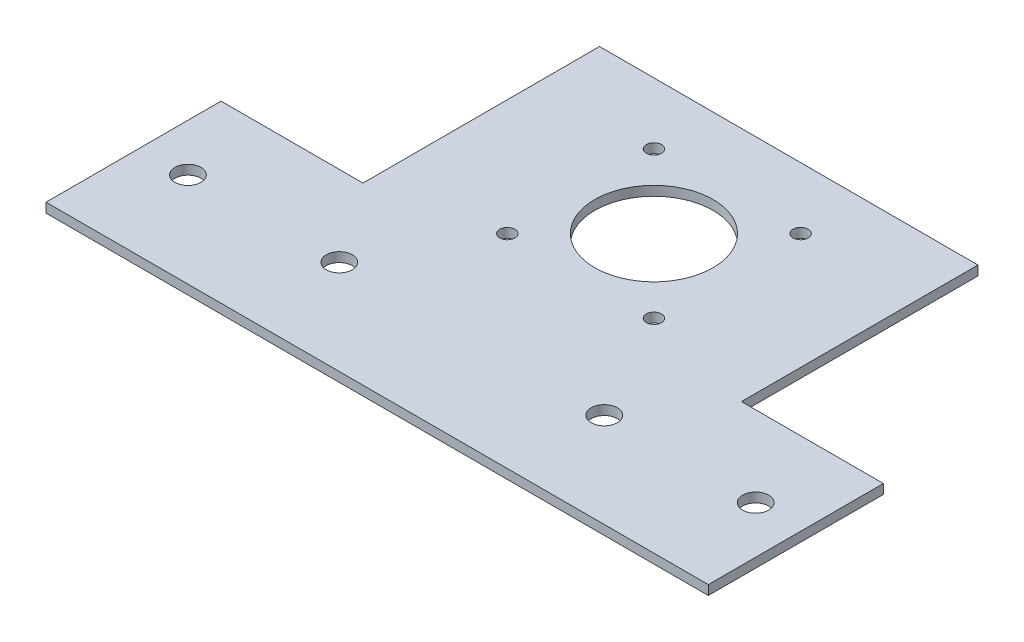
SolidWorks part; units mm, degrees
ref_plane "Plan de face" through (0, 0, 0) normal (0, 0, 1) x (1, 0, 0)
ref_plane "Plan de dessus" through (0, 0, 0) normal (0, 1, 0) x (1, 0, 0)
ref_plane "Plan de droite" through (0, 0, 0) normal (1, 0, 0) x (0, 0, -1)
sketch "Esquisse1" plane through (0, 0, 0) normal (0, 1, 0) x (1, 0, 0)
  line L0 (-23.5, 38.5) -> (23.5, -8.5) construction
  line L1 (-70, 43.5) -> (70, 43.5)
  line L2 (-70, 43.5) -> (-70, -43.5)
  line L3 (-70, -43.5) -> (70, -43.5)
  line L4 (70, 43.5) -> (70, -43.5)
  line L5 (-70, 43.5) -> (70, -43.5) construction
  line L6 (-70, -43.5) -> (70, 43.5) construction
  line L7 (-23.5, 38.5) -> (23.5, 38.5) construction
  line L8 (-23.5, 38.5) -> (-23.5, -8.5) construction
  line L9 (-23.5, -8.5) -> (23.5, -8.5) construction
  line L10 (23.5, 38.5) -> (23.5, -8.5) construction
  line L11 (-23.5, 38.5) -> (23.5, -8.5) construction
  line L12 (-23.5, -8.5) -> (23.5, 38.5) construction
  line L13 (23.5, 38.5) -> (-23.5, -8.5) construction
  line L14 (23.5, -8.5) -> (-23.5, 38.5) construction
  line L34 (-60, -23.5) -> (60, -23.5) construction
  line L35 (-15.5, 30.5) -> (15.5, 30.5) construction
  line L36 (-15.5, 30.5) -> (-15.5, -0.5) construction
  line L37 (-15.5, -0.5) -> (15.5, -0.5) construction
  line L38 (15.5, 30.5) -> (15.5, -0.5) construction
  line L39 (-15.5, 30.5) -> (15.5, -0.5) construction
  line L40 (-15.5, -0.5) -> (15.5, 30.5) construction
  circle A0 centre (23.5, 38.5) radius 2.6 construction
  circle A1 centre (23.5, -8.5) radius 2.6 construction
  circle A2 centre (-23.5, -8.5) radius 2.6 construction
  circle A3 centre (-23.5, 38.5) radius 2.6 construction
  circle A4 centre (-60, -23.5) radius 2.75
  circle A8 centre (0, 15) radius 19.5 construction
  circle A9 centre (-28, -23.5) radius 2.75
  circle A10 centre (28, -23.5) radius 2.75
  circle A11 centre (60, -23.5) radius 2.75
  circle A12 centre (-15.5, 30.5) radius 1.6
  circle A13 centre (15.5, 30.5) radius 1.6
  circle A14 centre (15.5, -0.5) radius 1.6
  circle A15 centre (-15.5, -0.5) radius 1.6
  circle A16 centre (0, 15) radius 12.5
  point P0 (0, 0)
  point P6 (0, 15)
  point P12 (0, 0)
  point P14 (0, -23.5)
  point P15 (0, 15)
  point P19 (-15, 15)
  point P27 (0, 15)
  point P28 (15, 15)
  point P29 (0, 30)
  point P43 (0, 38.5)
  point P53 (0, 15)
  dimension "D5" = 5.2
  dimension "D8" = 5.5
  dimension "D14" = 39
  dimension "D10" = 5.5
  dimension "D11" = 5.5
  dimension "D12" = 5.5
  dimension "D18" = 3.2
  dimension "D20" = 25
  dimension "D1" = 140
  dimension "D2" = 87
  dimension "D3" = 47
  dimension "D4" = 47
  dimension "D6" = 5
  dimension "D13" = 20
  dimension "D9" = 120
  dimension "D15" = 32
  dimension "D16" = 32
  dimension "D17" = 31
  dimension "D7" = 4
  dimension "D19" = 4
extrude "Boss.-Extru.1" add sketch "Esquisse1" along normal blind 2
sketch "Esquisse2" plane through (0, 2, 0) normal (0, 1, 0) x (1, 0, 0)
  line L0 (0, 43.5) -> (0, -43.5) construction
  line L1 (-70, 43.5) -> (-40, 43.5)
  line L2 (-70, 43.5) -> (-70, -6.5)
  line L3 (-70, -6.5) -> (-40, -6.5)
  line L4 (-40, 43.5) -> (-40, -6.5)
  line L5 (70, 43.5) -> (-70, 43.5) construction
  line L6 (-70, -43.5) -> (70, -43.5) construction
  line L7 (70, -6.5) -> (40, -6.5)
  line L8 (40, 43.5) -> (40, -6.5)
  line L9 (70, 43.5) -> (40, 43.5)
  line L10 (70, 43.5) -> (70, -6.5)
  dimension "D1" = 30
  dimension "D2" = 50
extrude "Enlèv. mat.-Extru.1" cut sketch "Esquisse2" against normal blind 10
equation "\"D10@Esquisse1\"=\"D8@Esquisse1\""
equation "\"D11@Esquisse1\"=\"D8@Esquisse1\""
equation "\"D12@Esquisse1\"=\"D8@Esquisse1\""
equation "\"D16@Esquisse1\"=\"D15@Esquisse1\""
